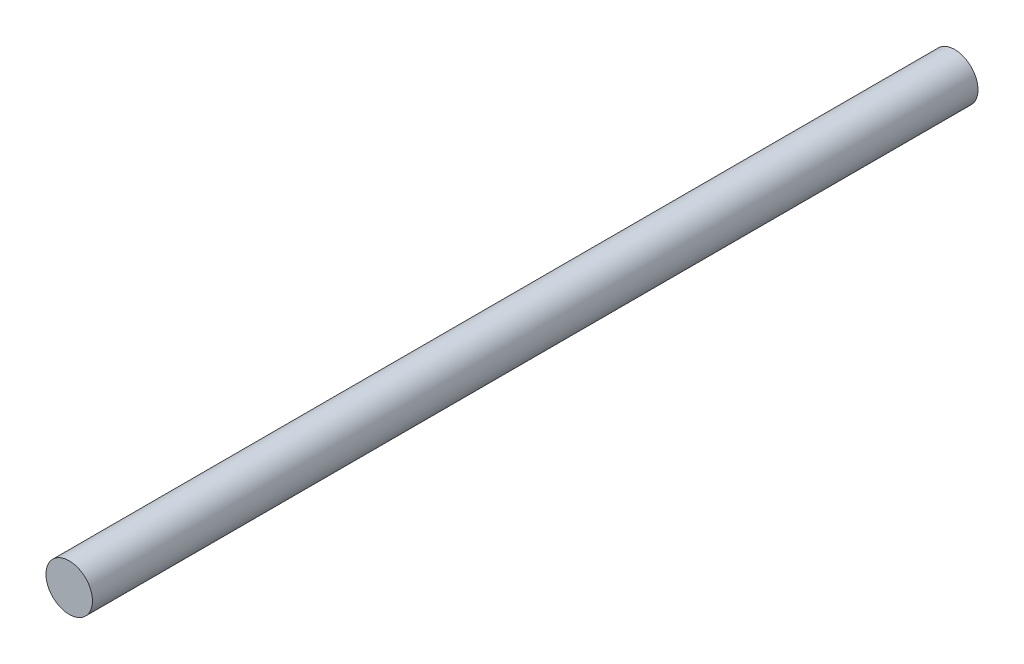
SolidWorks part; units mm, degrees
ref_plane "前视基准面" through (0, 0, 0) normal (0, 0, 1) x (1, 0, 0)
ref_plane "上视基准面" through (0, 0, 0) normal (0, 1, 0) x (1, 0, 0)
ref_plane "右视基准面" through (0, 0, 0) normal (1, 0, 0) x (0, 0, -1)
other "Configuration Table"
sketch "草图1" plane through (0, 0, 0) normal (0, 0, 1) x (1, 0, 0)
  circle A0 centre (0, 0) radius 2.1
extrude "凸台-拉伸1" add sketch "草图1" along normal blind 80
